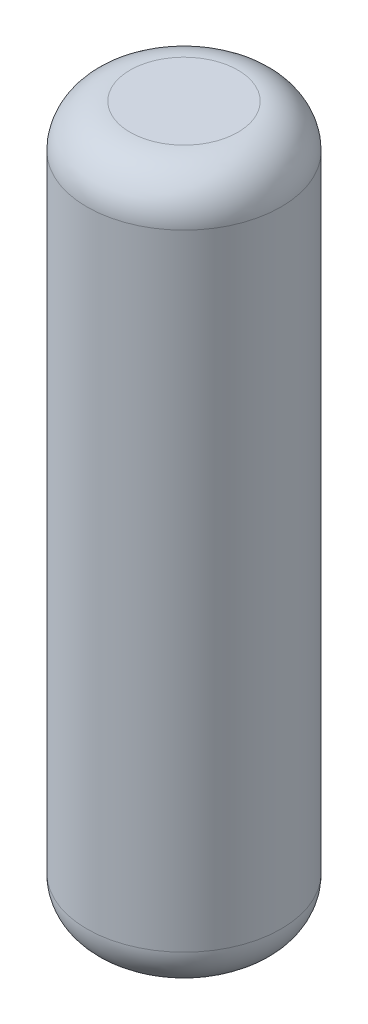
SolidWorks part; units mm, degrees
ref_plane "Front Plane" through (0, 0, 0) normal (0, 0, 1) x (1, 0, 0)
ref_plane "Top Plane" through (0, 0, 0) normal (0, 1, 0) x (1, 0, 0)
ref_plane "Right Plane" through (0, 0, 0) normal (1, 0, 0) x (0, 0, -1)
sketch "Sketch1" plane through (0, 0, 0) normal (0, 1, 0) x (1, 0, 0)
  circle A0 centre (0, 0) radius 2.25
  dimension "D1" = 4.5
extrude "Boss-Extrude1" add sketch "Sketch1" along normal blind 16.5
fillet "Fillet2" radius 1 2 edges at (0, 0, 2.25) (0, 16.5, 2.25)
